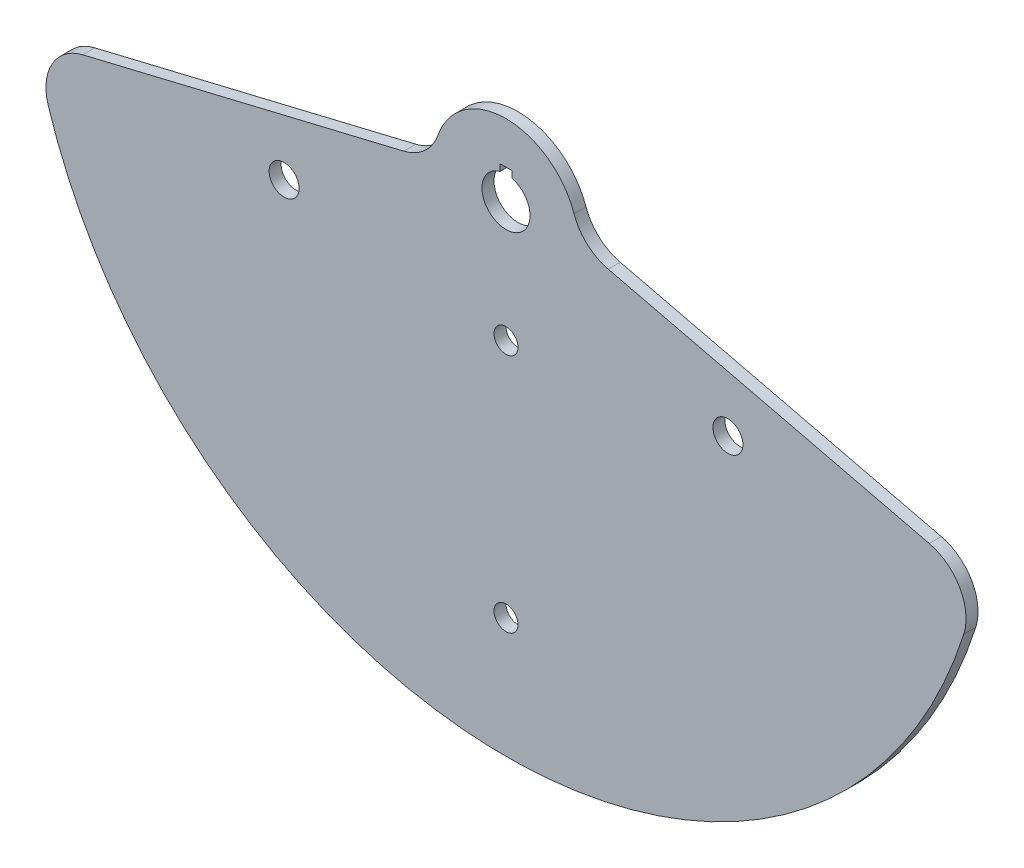
SolidWorks part; units mm, degrees
material "AISI 1020"
ref_plane "Front Plane" through (0, 0, 0) normal (0, 0, 1) x (1, 0, 0)
ref_plane "Top Plane" through (0, 0, 0) normal (0, 1, 0) x (1, 0, 0)
ref_plane "Right Plane" through (0, 0, 0) normal (1, 0, 0) x (0, 0, -1)
sketch "Sketch5" plane through (0, 0, 0) normal (0, 0, 1) x (1, 0, 0)
  line L0 (-223.7799, -44.5778) -> (-54.0427, -3.8275)
  line L1 (-38.1, 0) -> (38.1, 0) construction
  line L2 (54.0427, -3.8275) -> (223.7799, -44.5778)
  line L3 (0, 0) -> (-117.3327, -48.6008) construction
  line L4 (0, 0) -> (0, -254) construction
  line L5 (117.3327, -48.6008) -> (0, 0) construction
  line L6 (-117.3327, -48.6008) -> (117.3327, -48.6008) construction
  arc A0 (-242.056, -76.9733) -> (242.056, -76.9733) centre (0, 0) ccw
  circle A2 centre (0, 0) radius 12.7
  arc A3 (35.9833, 12.5224) -> (-35.9833, 12.5224) centre (0, 0) ccw
  circle A4 centre (-117.3327, -48.6008) radius 7.9375
  circle A5 centre (117.3327, -48.6008) radius 7.9375
  arc A6 (54.0427, -3.8275) -> (35.9833, 12.5224) centre (59.9722, 20.8707) cw
  arc A7 (-54.0427, -3.8275) -> (-35.9833, 12.5224) centre (-59.9722, 20.8707) ccw
  arc A8 (-223.7799, -44.5778) -> (-242.056, -76.9733) centre (-217.8504, -69.276) ccw
  arc A9 (223.7799, -44.5778) -> (242.056, -76.9733) centre (217.8504, -69.276) cw
  dimension "D1" = 508
  dimension "D2" = 153
  dimension "D3" = 25.4
  dimension "D5" = 15.875
  dimension "D8" = 25.4
  dimension "D4" = 25.4
  dimension "D10" = 25.4
  dimension "D6" = 135
  dimension "D9" = 127
extrude "Boss-Extrude2" add sketch "Sketch5" along normal mid plane 6.35 separate body
sketch "Sketch8" plane through (0, 0, 0) normal (0, 0, 1) x (1, 0, 0)
  line L0 (0, 0) -> (0, 12.7) construction
  line L2 (3.175, 9.525) -> (-3.175, 9.525)
  line L3 (3.175, 9.525) -> (3.175, 15.875)
  line L4 (3.175, 15.875) -> (-3.175, 15.875)
  line L5 (-3.175, 9.525) -> (-3.175, 15.875)
  line L6 (3.175, 9.525) -> (-3.175, 15.875) construction
  line L7 (3.175, 15.875) -> (-3.175, 9.525) construction
  circle A0 centre (0, 0) radius 12.7 construction
  arc A1 (3.175, 12.2967) -> (-3.175, 12.2967) centre (0, 0) ccw
  dimension "D1" = 6.35
  dimension "D2" = 6.35
extrude "Cut-Extrude1" cut sketch "Sketch8" against normal through all both and the other way through all contours L4 L5 L2 L3
sketch "Sketch9" plane through (0, 0, 0) normal (0, 0, 1) x (1, 0, 0)
  line L0 (0, 0) -> (0, -254) construction
  arc A0 (-242.056, -76.9733) -> (242.056, -76.9733) centre (0, 0) ccw construction
  circle A1 centre (0, -63.5) radius 6.35
  circle A2 centre (0, -190.5) radius 6.35
  dimension "D1" = 12.7
  dimension "D2" = 63.5
  dimension "D3" = 127
extrude "Cut-Extrude2" cut sketch "Sketch9" against normal through all both and the other way through all
